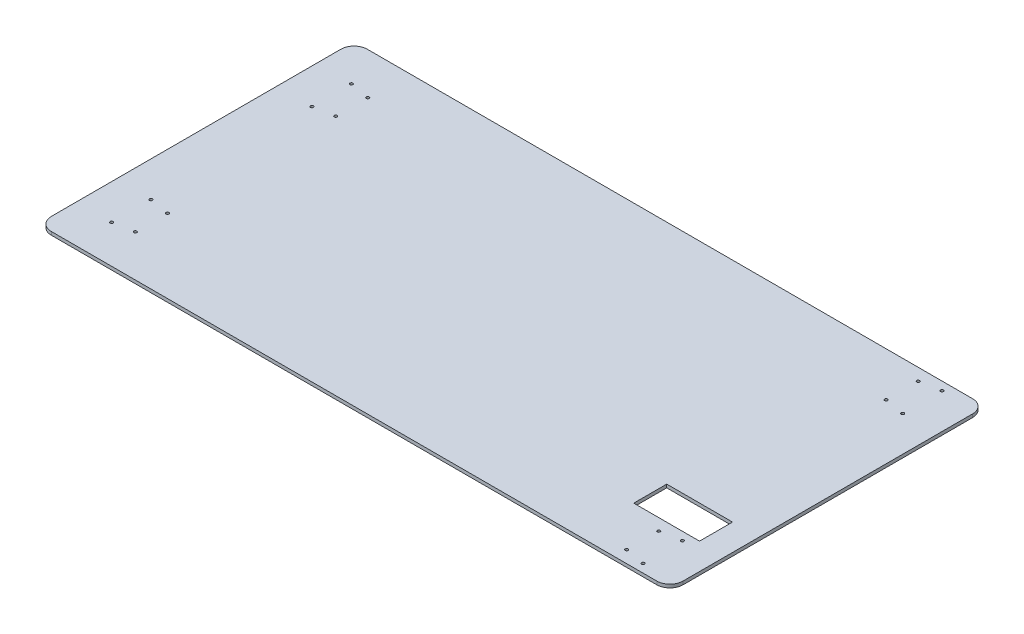
SolidWorks part; units mm, degrees
material "cherry wood"
ref_plane "Front Plane" through (0, 0, 0) normal (0, 0, 1) x (1, 0, 0)
ref_plane "Top Plane" through (0, 0, 0) normal (0, 1, 0) x (1, 0, 0)
ref_plane "Right Plane" through (0, 0, 0) normal (1, 0, 0) x (0, 0, -1)
sketch "Sketch2" plane through (0, 0, 0) normal (0, 1, 0) x (1, 0, 0)
  line L1 (-609.6, 304.8) -> (609.6, 304.8)
  line L2 (-609.6, 304.8) -> (-609.6, -304.8)
  line L3 (-609.6, -304.8) -> (609.6, -304.8)
  line L4 (609.6, 304.8) -> (609.6, -304.8)
  line L5 (0, -304.8) -> (0, 304.8) construction
  line L6 (-609.6, 0) -> (609.6, 0) construction
  line L7 (558.8, -196.85) -> (431.8, -196.85)
  line L8 (558.8, -196.85) -> (558.8, -133.1551)
  line L9 (558.8, -133.1551) -> (431.8, -133.1551)
  line L10 (431.8, -196.85) -> (431.8, -133.1551)
  line L11 (495.3, -133.1551) -> (495.3, -196.85) construction
  line L12 (558.8, -165.0025) -> (431.8, -165.0025) construction
  circle A33 centre (541.528, 288.544) radius 2.794
  circle A36 centre (541.528, 212.598) radius 2.794
  circle A37 centre (502.666, 219.456) radius 2.794
  circle A38 centre (502.666, 281.432) radius 2.794
  circle A41 centre (502.666, -281.432) radius 2.794
  circle A42 centre (502.666, -219.456) radius 2.794
  circle A43 centre (541.528, -212.598) radius 2.794
  circle A46 centre (541.528, -288.544) radius 2.794
  circle A48 centre (-541.528, 155.448) radius 2.794
  circle A51 centre (-502.666, 224.282) radius 2.794
  circle A52 centre (-541.528, 231.394) radius 2.794
  circle A53 centre (-502.666, 162.306) radius 2.794
  circle A58 centre (-502.666, -162.306) radius 2.794
  circle A59 centre (-541.528, -231.394) radius 2.794
  circle A60 centre (-502.666, -224.282) radius 2.794
  circle A63 centre (-541.528, -155.448) radius 2.794
  point P0 (0, 0)
  point P6 (495.3, -165.0025)
  dimension "D8" = 23.368
  dimension "D9" = 106.934
  dimension "D10" = 107.95
  dimension "D14" = 106.934
  dimension "D15" = 85.344
  dimension "D16" = 68.072
  dimension "D17" = 92.202
  dimension "D4" = 127
  dimension "D5" = 50.8
  dimension "D6" = 16.256
  dimension "D7" = 68.072
  dimension "D25" = 73.406
  dimension "D26" = 68.072
  dimension "D27" = 149.352
  dimension "D28" = 68.072
  dimension "D29" = 142.494
  dimension "D30" = 106.934
  dimension "D31" = 80.518
  dimension "D1" = 1219.2
  dimension "D2" = 609.6
extrude "Boss-Extrude1" add sketch "Sketch2" along normal blind 6.35
fillet "Fillet1" radius 25.4 4 edges at (609.6, 3.175, 304.8) (609.6, 3.175, -304.8) (-609.6, 3.175, -304.8) (-609.6, 3.175, 304.8)
